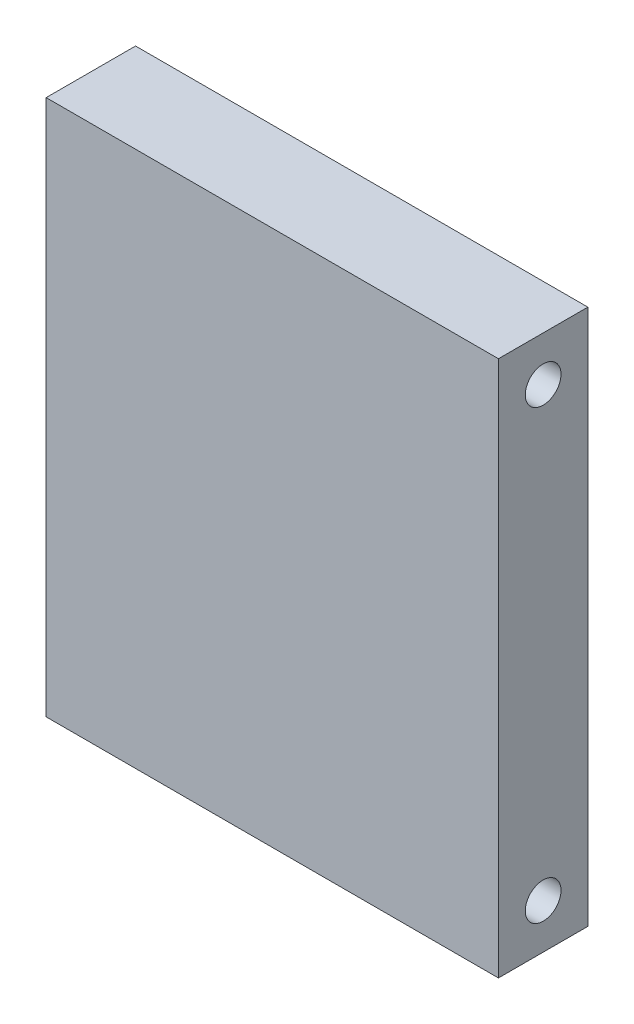
SolidWorks part; units mm, degrees
ref_plane "Front" through (0, 0, 0) normal (0, 0, 1) x (1, 0, 0)
ref_plane "Top" through (0, 0, 0) normal (0, 1, 0) x (1, 0, 0)
ref_plane "Right" through (0, 0, 0) normal (1, 0, 0) x (0, 0, -1)
sketch "Sketch1" plane through (0, 0, 0) normal (0, 0, 1) x (1, 0, 0)
  line L1 (0, 0) -> (50.6, 0)
  line L2 (0, 0) -> (0, 60)
  line L3 (0, 60) -> (50.6, 60)
  line L4 (50.6, 0) -> (50.6, 60)
  dimension "D1" = 50.6
  dimension "D2" = 60
extrude "Extrude1" add sketch "Sketch1" along normal blind 10
sketch "Sketch2" plane through (0, 0, 0) normal (-1, 0, 0) x (0, 0, 1)
  circle A0 centre (5, 55) radius 2
  circle A1 centre (5, 5) radius 2
extrude "Cut-Extrude1" cut sketch "Sketch2" against normal blind 50.6
